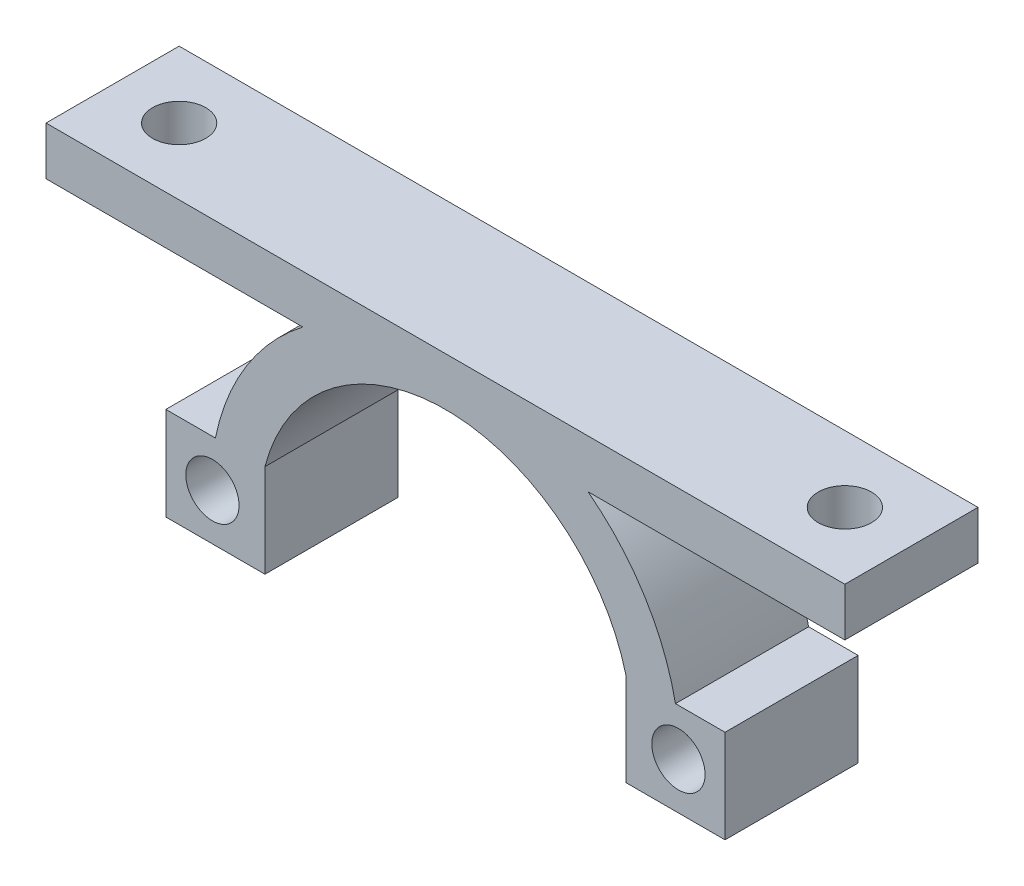
SolidWorks part; units mm, degrees
ref_plane "Plan de face" through (0, 0, 0) normal (0, 0, 1) x (1, 0, 0)
ref_plane "Plan de dessus" through (0, 0, 0) normal (0, 1, 0) x (1, 0, 0)
ref_plane "Plan de droite" through (0, 0, 0) normal (1, 0, 0) x (0, 0, -1)
sketch "Esquisse1" plane through (0, 0, 0) normal (0, 0, 1) x (1, 0, 0)
  line L0 (-21, 0) -> (21, 0) construction
  line L1 (-21, 3.5) -> (21, 3.5) construction
  line L2 (-21, 3.5) -> (-21, -3.5)
  line L3 (-21, -3.5) -> (21, -3.5) construction
  line L4 (21, 3.5) -> (21, -3.5)
  line L5 (-21, 3.5) -> (-13.5554, 3.5) construction
  line L6 (13.5554, 3.5) -> (21, 3.5) construction
  line L7 (-13.5554, 3.5) -> (-13.5554, -3.5)
  line L8 (-13.5554, -3.5) -> (-21, -3.5)
  line L9 (21, -3.5) -> (13.5554, -3.5)
  line L10 (13.5554, 3.5) -> (13.5554, -3.5)
  line L11 (0, 0) -> (0, 17.6287) construction
  line L12 (-17.2777, 3.5) -> (-21, 3.5)
  line L13 (17.2777, 3.5) -> (21, 3.5)
  circle A0 centre (0, 0) radius 14 construction
  circle A1 centre (-17.5, 0) radius 2
  circle A2 centre (17.5, 0) radius 2
  arc A3 (-13.5554, 3.5) -> (13.5554, 3.5) centre (0, 0) cw
  arc A4 (-17.2777, 3.5) -> (17.2777, 3.5) centre (0, 0) cw
  point P13 (0, 0)
  dimension "D1" = 28
  dimension "D4" = 4
  dimension "D5" = 4
  dimension "D6" = 3.5
  dimension "D7" = 3.5
  dimension "D8" = 0
  dimension "D2" = 42
  dimension "D3" = 7
extrude "Boss.-Extru.1" add sketch "Esquisse1" along normal blind 10
sketch "Esquisse3" plane through (0, 0, 0) normal (0, 0, 1) x (1, 0, 0)
  line L0 (0, 17.6287) -> (0, 14) construction
  line L2 (-30, 17.6287) -> (30, 17.6287)
  line L3 (-30, 17.6287) -> (-30, 14)
  line L4 (-30, 14) -> (30, 14)
  line L5 (30, 17.6287) -> (30, 14)
  arc A0 (17.2777, 3.5) -> (-17.2777, 3.5) centre (0, 0) ccw construction
  arc A1 (13.5554, 3.5) -> (-13.5554, 3.5) centre (0, 0) ccw construction
  point P12 (0, 17.6287)
  dimension "D1" = 3.6287
  dimension "D2" = 60
extrude "Boss.-Extru.2" add sketch "Esquisse3" along normal blind 10
sketch "Esquisse4" plane through (0, 17.6287, 0) normal (0, 1, 0) x (1, 0, 0)
  line L0 (-30, -5) -> (30, -5) construction
  line L1 (-30, -10) -> (-30, 0) construction
  line L2 (30, -10) -> (30, 0) construction
  circle A0 centre (-25, -5) radius 2
  circle A1 centre (25, -5) radius 2
  dimension "D1" = 4
  dimension "D2" = 4
  dimension "D3" = 5
  dimension "D4" = 5
extrude "Enlèv. mat.-Extru.1" cut sketch "Esquisse4" against normal up to next
